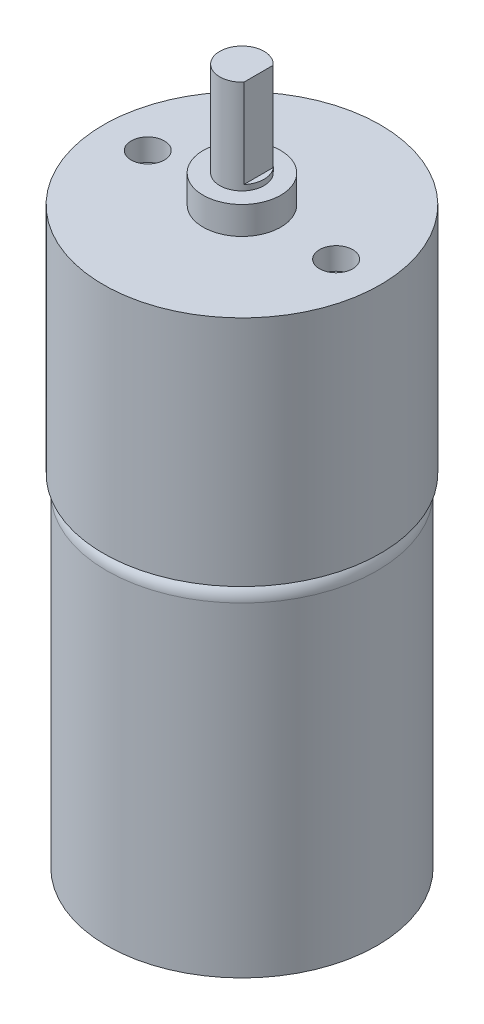
SolidWorks part; units mm, degrees
ref_plane "Přední rovina" through (0, 0, 0) normal (0, 0, 1) x (1, 0, 0)
ref_plane "Horní rovina" through (0, 0, 0) normal (0, 1, 0) x (1, 0, 0)
ref_plane "Pravá rovina" through (0, 0, 0) normal (1, 0, 0) x (0, 0, -1)
sketch "Skica1" plane through (0, 0, 0) normal (0, 0, 1) x (1, 0, 0)
  line L0 (0, 0) -> (0, 84.5603) construction
  line L1 (0, 0) -> (3.25, 0)
  line L2 (3.25, 0) -> (3.25, 2)
  line L3 (3.25, 2) -> (12.2, 2)
  line L4 (12.2, 2) -> (12.2, 31.3)
  line L7 (10.7, 32.8) -> (12.5, 32.8)
  line L8 (12.5, 53.8) -> (3.5, 53.8)
  line L9 (3.5, 53.8) -> (3.5, 56.3)
  line L10 (3.5, 56.3) -> (2, 56.3)
  line L11 (2, 56.3) -> (2, 64.8)
  line L12 (2, 64.8) -> (0, 64.8)
  line L13 (12.5, 32.8) -> (12.5, 53.8)
  line L14 (0, 0) -> (0, 64.8)
  arc A0 (12.2, 31.3) -> (10.7, 32.8) centre (10.7, 31.3) ccw
  point P7 (13.2931, 69.0048)
  point P9 (0, 0)
  point P15 (3.25, 1)
  point P18 (0, 0)
  point P23 (0, 0)
  point P24 (0, 0)
  point P25 (0, 0)
  point P26 (0, 0)
  dimension "D5" = 1.5
  dimension "D1" = 6.5
  dimension "D2" = 2
  dimension "D3" = 24.4
  dimension "D6" = 25
  dimension "D7" = 21
  dimension "D8" = 7
  dimension "D9" = 2.5
  dimension "D10" = 8.5
  dimension "D11" = 4
revolve "Rotovat1" add sketch "Skica1" angle 360 about L0
sketch "Skica2" plane through (0, 64.8, 0) normal (0, 1, 0) x (1, 0, 0)
  line L0 (1.5, 1.3229) -> (1.5, -1.3229)
  circle A0 centre (0, 0) radius 2 construction
  arc A1 (1.5, -1.3229) -> (1.5, 1.3229) centre (0, 0) ccw
  dimension "D1" = 1.5
extrude "Odebrat vysunutím1" cut sketch "Skica2" against normal blind 8
sketch "Skica3" plane through (0, 53.8, 0) normal (0, 1, 0) x (1, 0, 0)
  line L0 (0, 4.8812) -> (0, -4.1047) construction
  circle A0 centre (8.5, 0) radius 1.5
  circle A1 centre (-8.5, 0) radius 1.5
  dimension "D1" = 3
  dimension "D2" = 8.5
extrude "Odebrat vysunutím2" cut sketch "Skica3" against normal blind 2
